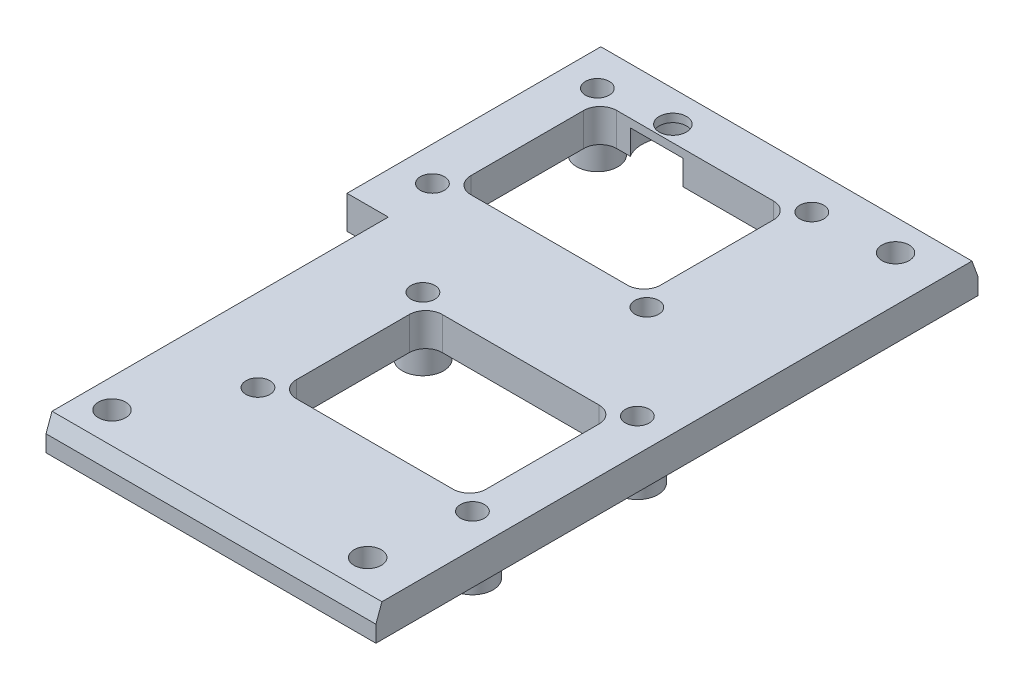
SolidWorks part; units mm, degrees
ref_plane "Спереди" through (0, 0, 0) normal (0, 0, 1) x (1, 0, 0)
ref_plane "Сверху" through (0, 0, 0) normal (0, 1, 0) x (1, 0, 0)
ref_plane "Справа" through (0, 0, 0) normal (1, 0, 0) x (0, 0, -1)
sketch "Sketch1" plane through (0, 0, 0) normal (0, 1, 0) x (1, 0, 0)
  line L0 (-22.5, 32) -> (22.5, 32) construction
  line L1 (22.5, -37) -> (-22.5, -37)
  line L2 (22.5, -37) -> (22.5, 37)
  line L3 (22.5, 37) -> (-22.5, 37)
  line L4 (-22.5, -37) -> (-22.5, 37)
  line L5 (22.5, -37) -> (-22.5, 37) construction
  line L6 (22.5, 37) -> (-22.5, -37) construction
  line L7 (22.5, -32) -> (-22.5, -32) construction
  circle A0 centre (-10, 32) radius 1.65
  circle A1 centre (17, 32) radius 1.65
  circle A2 centre (-14, -32) radius 1.65
  circle A3 centre (17, -32) radius 1.65
  point P0 (0, 0)
  point P18 (0, 32)
  point P19 (0, -32)
  dimension "D5" = 3.3
  dimension "D1" = 45
  dimension "D2" = 74
  dimension "D3" = 5
  dimension "D4" = 5
  dimension "D6" = 17
  dimension "D7" = 10
  dimension "D8" = 17
  dimension "D9" = 14
extrude "Boss-Extrude1" add sketch "Sketch1" along normal blind 4
sketch "Sketch3" plane through (0, 0, 0) normal (0, -1, 0) x (1, 0, 0)
  circle A0 centre (-10, -32) radius 3.75
  dimension "D1" = 7.5
extrude "Cut-Extrude2" cut sketch "Sketch3" against normal blind 3
sketch "Sketch4" plane through (0, 0, 0) normal (0, -1, 0) x (1, 0, 0)
  line L0 (-17.5, 37) -> (-17.5, -5)
  line L1 (-22.5, 37) -> (22.5, 37) construction
  line L2 (-17.5, -5) -> (-22.5, -5)
  line L3 (-22.5, -37) -> (-22.5, 37) construction
  line L4 (-22.5, -5) -> (-22.5, 37)
  line L5 (-22.5, 37) -> (-17.5, 37)
  dimension "D1" = 5
  dimension "D2" = 42
extrude "Cut-Extrude3" cut sketch "Sketch4" against normal through all
sketch "Sketch6" plane through (0, 0, 0) normal (0, -1, 0) x (1, 0, 0)
  line L0 (22.5, 37) -> (22.5, 36.5)
  line L1 (22.5, 37) -> (22.5, -37) construction
  line L2 (22.5, 36.5) -> (-17.5, 36.5)
  line L3 (-17.5, -5) -> (-17.5, 37) construction
  line L4 (-17.5, 36.5) -> (-17.5, 37)
  line L5 (-17.5, 37) -> (22.5, 37)
  line L6 (22.5, -36.5) -> (-22.5, -36.5)
  line L7 (-22.5, -37) -> (-22.5, -5) construction
  line L8 (-22.5, -36.5) -> (-22.5, -37)
  line L9 (-22.5, -37) -> (22.5, -37)
  line L10 (22.5, -37) -> (22.5, -36.5)
  dimension "D1" = 0.5
  dimension "D2" = 0.5
extrude "Cut-Extrude4" cut sketch "Sketch6" against normal through all
chamfer "Chamfer1" distance 2 angle 20 2 edges at (0, 4, -36.5) (2.5, 4, 36.5)
sketch "Sketch7" plane through (0, 0, 0) normal (0, -1, 0) x (1, 0, 0)
  line L0 (-22.5, -36.5) -> (-22.5, -5) construction
  line L1 (7.65, -11.2) -> (-18.35, -11.2) construction
  line L2 (7.65, -11.2) -> (7.65, -31.2) construction
  line L3 (7.65, -31.2) -> (-18.35, -31.2) construction
  line L4 (-18.35, -11.2) -> (-18.35, -31.2) construction
  line L5 (7.65, -11.2) -> (-18.35, -31.2) construction
  line L6 (7.65, -31.2) -> (-18.35, -11.2) construction
  line L7 (18.5, 20.8) -> (-7.5, 20.8) construction
  line L8 (18.5, 20.8) -> (18.5, 0.8) construction
  line L9 (18.5, 0.8) -> (-7.5, 0.8) construction
  line L10 (-7.5, 20.8) -> (-7.5, 0.8) construction
  line L11 (18.5, 20.8) -> (-7.5, 0.8) construction
  line L12 (18.5, 0.8) -> (-7.5, 20.8) construction
  line L14 (-22.5, -5) -> (-17.5, -5) construction
  line L15 (-17.5, -5) -> (-17.5, 36.5) construction
  line L16 (6.15, -12.3538) -> (-16.85, -12.3538)
  line L17 (6.15, -12.3538) -> (6.15, -30.0462)
  line L18 (6.15, -30.0462) -> (-16.85, -30.0462)
  line L19 (-16.85, -12.3538) -> (-16.85, -30.0462)
  line L20 (6.15, -12.3538) -> (-16.85, -30.0462) construction
  line L21 (6.15, -30.0462) -> (-16.85, -12.3538) construction
  line L22 (17, 19.6462) -> (-6, 19.6462)
  line L23 (17, 19.6462) -> (17, 1.9538)
  line L24 (17, 1.9538) -> (-6, 1.9538)
  line L25 (-6, 19.6462) -> (-6, 1.9538)
  line L26 (17, 19.6462) -> (-6, 1.9538) construction
  line L27 (17, 1.9538) -> (-6, 19.6462) construction
  line L28 (-22.5, -21.2) -> (22.5, -21.2) construction
  line L29 (22.5, 36.5) -> (22.5, -36.5) construction
  line L30 (-17.5, 10.8) -> (22.5, 10.8) construction
  line L31 (-17.5, 36.5) -> (22.5, 36.5) construction
  circle A0 centre (-18.35, -31.2) radius 1.45
  circle A1 centre (-18.35, -11.2) radius 1.45
  circle A2 centre (7.65, -11.2) radius 1.45
  circle A3 centre (7.65, -31.2) radius 1.45
  circle A4 centre (18.5, 0.8) radius 1.45
  circle A5 centre (-7.5, 0.8) radius 1.45
  circle A6 centre (-7.5, 20.8) radius 1.45
  circle A7 centre (18.5, 20.8) radius 1.45
  point P0 (-5.35, -21.2)
  point P5 (5.5, 10.8)
  point P24 (-5.35, -21.2)
  point P29 (5.5, 10.8)
  dimension "D7" = 2.9
  dimension "D1" = 20
  dimension "D2" = 26
  dimension "D3" = 4.15
  dimension "D4" = 16.2
  dimension "D5" = 25.7
  dimension "D6" = 10
  dimension "D8" = 23
extrude "Cut-Extrude5" cut sketch "Sketch7" against normal through all
fillet "Fillet1" radius 2 8 edges at (17, 2, 19.6462) (17, 2, 1.9538) (-6, 2, 1.9538) (-6, 2, 19.6462) (6.15, 2, -30.0462) (6.15, 2, -12.3538) (-16.85, 2, -12.3538) (-16.85, 2, -30.0462)
sketch "Sketch8" plane through (0, 0, 0) normal (0, -1, 0) x (1, 0, 0)
  circle A0 centre (-18.35, -11.2) radius 2.5
  circle A1 centre (-18.35, -31.2) radius 2.5
  circle A2 centre (7.65, -11.2) radius 2.5
  circle A3 centre (7.65, -31.2) radius 2.5
  circle A4 centre (18.5, 0.8) radius 2.5
  circle A5 centre (-7.5, 0.8) radius 2.5
  circle A6 centre (-7.5, 20.8) radius 2.5
  circle A7 centre (18.5, 20.8) radius 2.5
  circle A8 centre (-18.35, -31.2) radius 1.45
  circle A9 centre (-18.35, -11.2) radius 1.45
  circle A10 centre (-7.5, 0.8) radius 1.45
  circle A11 centre (-7.5, 20.8) radius 1.45
  circle A12 centre (18.5, 20.8) radius 1.45
  circle A13 centre (18.5, 0.8) radius 1.45
  circle A14 centre (7.65, -11.2) radius 1.45
  circle A15 centre (7.65, -31.2) radius 1.45
  dimension "D1" = 5
  dimension "D2" = 2.9
extrude "Boss-Extrude2" add sketch "Sketch8" along normal blind 3
